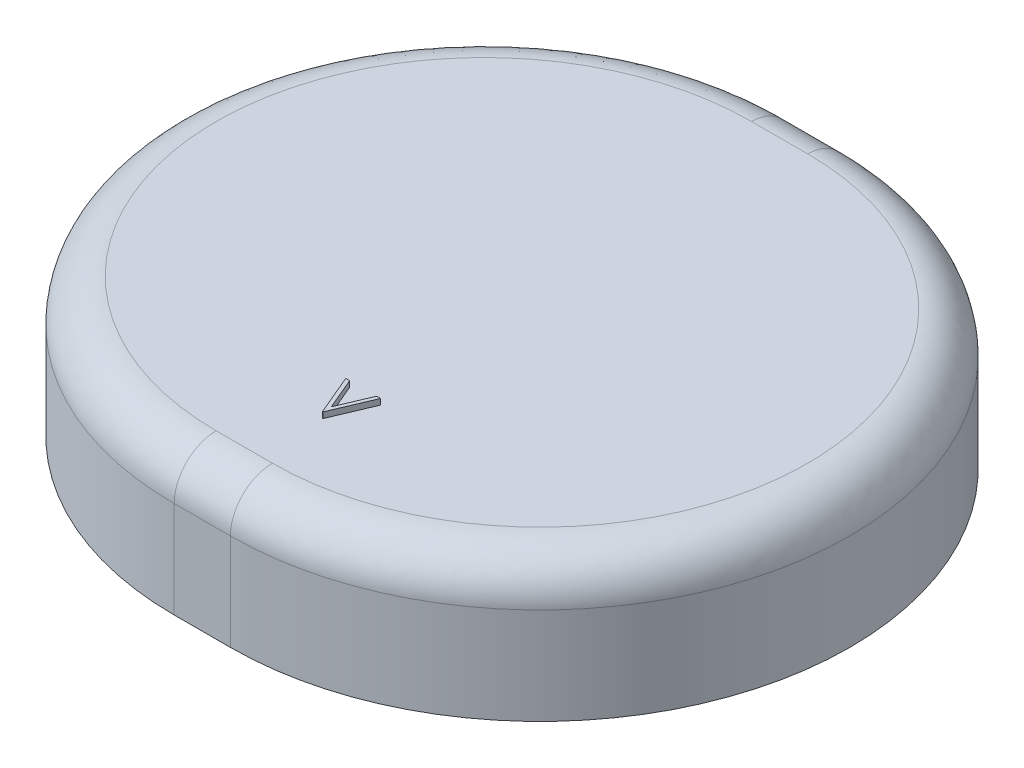
SolidWorks part; units mm, degrees
ref_plane "Front Plane" through (0, 0, 0) normal (0, 0, 1) x (1, 0, 0)
ref_plane "Top Plane" through (0, 0, 0) normal (0, 1, 0) x (1, 0, 0)
ref_plane "Right Plane" through (0, 0, 0) normal (1, 0, 0) x (0, 0, -1)
sketch "Sketch1" plane through (0, -28.1568, 0) normal (0, 1, 0) x (1, 0, 0)
  line L0 (1.0326, 27.9552) -> (-3.8376, 27.954)
  line L1 (-3.8248, -23.7126) -> (1.0453, -23.7114)
  arc A0 (-3.8376, 27.954) -> (-3.8248, -23.7126) centre (-3.8312, 2.1207) ccw
  arc A1 (1.0453, -23.7114) -> (1.0326, 27.9552) centre (1.0389, 2.1219) ccw
sketch "Sketch2" plane through (0, 0, 0) normal (1, 0, 0) x (0, 0, -1)
  line L0 (27.9546, -28.1568) -> (27.9546, -19.7953)
  line L1 (25.316, -17.1568) -> (3.4134, -17.1568)
  line L2 (3.4134, -17.1568) -> (3.4134, -16.1568)
  line L3 (3.4134, -16.1568) -> (25.316, -16.1568)
  line L4 (28.9546, -19.7953) -> (28.9546, -28.1568)
  line L5 (28.9546, -28.1568) -> (27.9546, -28.1568)
  line L6 (27.9552, -28.1568) -> (-23.7114, -28.1568) construction
  line L7 (27.9552, -28.1568) -> (27.954, -28.1568) construction
  arc A0 (27.9546, -19.7953) -> (25.316, -17.1568) centre (25.316, -19.7953) ccw
  arc A1 (25.316, -16.1568) -> (28.9546, -19.7953) centre (25.316, -19.7953) cw
  dimension "D1" = 1
  dimension "D2" = 11
sweep "Sweep1" add profiles "Sketch2" path "Sketch1"
sketch "Sketch3" plane through (-0.0008, 0, -3.4134) normal (0.0002, 0, 1) x (1, 0, -0.0002)
  line L0 (-7.8977, -16.1568) -> (4.4356, -16.1568)
  line L1 (-7.8977, -16.1568) -> (-7.8977, -17.1568)
  line L2 (-7.8977, -17.1568) -> (4.4356, -17.1568)
  line L3 (4.4356, -17.1568) -> (4.4356, -16.1568)
  line L4 (-3.8367, -16.1568) -> (1.0334, -16.1568) construction
  line L5 (-3.8367, -17.1568) -> (1.0334, -17.1568) construction
extrude "Boss-Extrude1" add sketch "Sketch3" along normal blind 4 and the other way blind 1
sketch3d "cap centerline"
  line L0 (-1.4025, -16.1568, 21.309) -> (-1.4025, -16.1568, -25.3157) construction
  line L2 (1.0326, -16.1568, -25.3163) -> (-3.8376, -16.1568, -25.3151) construction
  line L3 (-1.4025, -16.1568, -2.0033) -> (-1.4025, 28.2782, -2.0033) construction
sketch "Sketch4" plane through (0, -16.1568, 0) normal (0, 1, 0) x (1, 0, 0)
  text T0 "V"
extrude "Boss-Extrude2" add sketch "Sketch4" along normal blind 0.5
